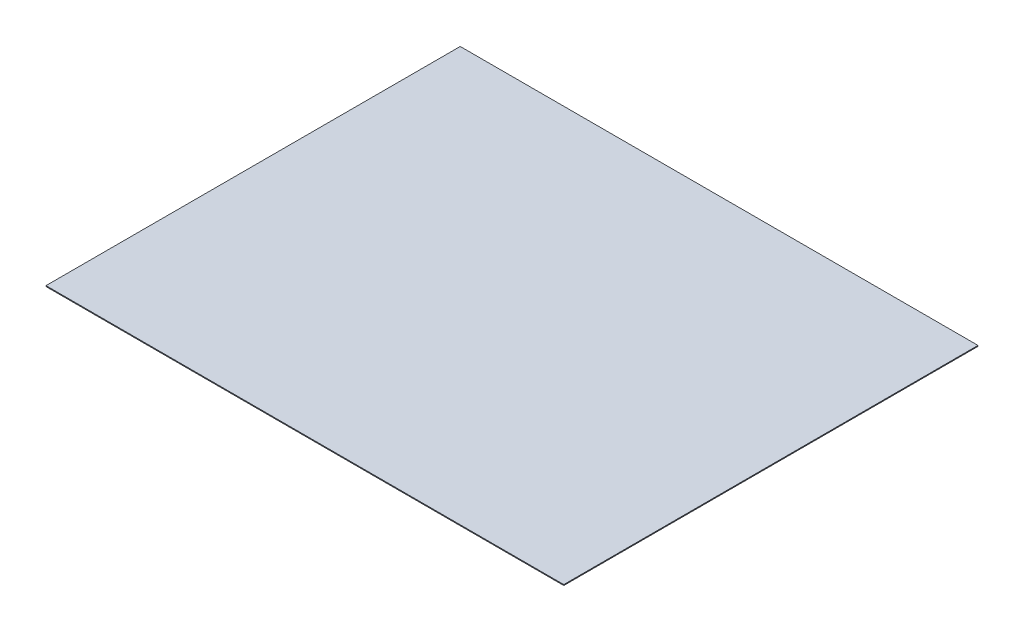
SolidWorks part; units mm, degrees
ref_plane "Front Plane" through (0, 0, 0) normal (0, 0, 1) x (1, 0, 0)
ref_plane "Top Plane" through (0, 0, 0) normal (0, 1, 0) x (1, 0, 0)
ref_plane "Right Plane" through (0, 0, 0) normal (1, 0, 0) x (0, 0, -1)
sketch "Sketch1" plane through (0, 0, 0) normal (0, 1, 0) x (1, 0, 0)
  line L1 (-593.1243, 197.7081) -> (930.8757, 197.7081)
  line L2 (-593.1243, 197.7081) -> (-593.1243, -1021.4919)
  line L3 (-593.1243, -1021.4919) -> (930.8757, -1021.4919)
  line L4 (930.8757, 197.7081) -> (930.8757, -1021.4919)
  dimension "D1" = 1219.2
  dimension "D2" = 1524
extrude "Boss-Extrude1" add sketch "Sketch1" along normal blind 2.54
